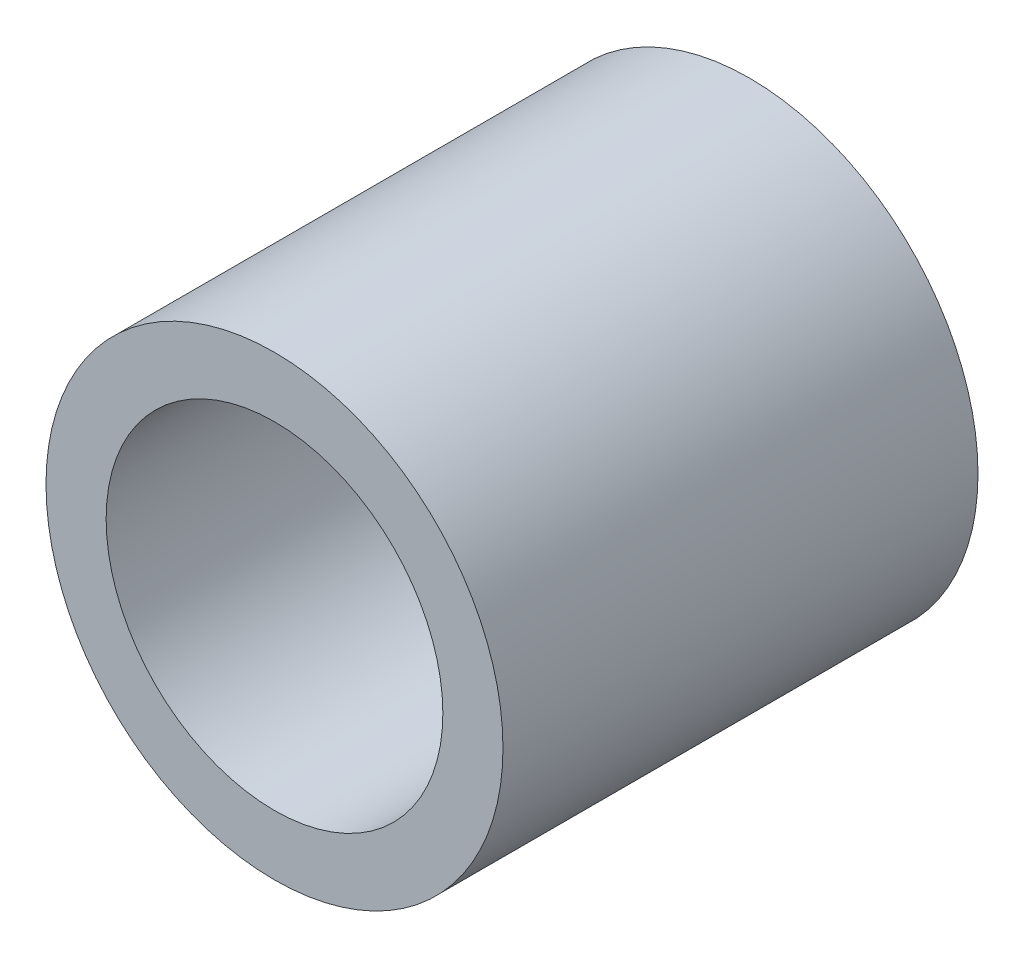
SolidWorks part; units mm, degrees
ref_plane "Front Plane" through (0, 0, 0) normal (0, 0, 1) x (1, 0, 0)
ref_plane "Top Plane" through (0, 0, 0) normal (0, 1, 0) x (1, 0, 0)
ref_plane "Right Plane" through (0, 0, 0) normal (1, 0, 0) x (0, 0, -1)
sketch "Sketch1" plane through (0, 0, 0) normal (0, 0, 1) x (1, 0, 0)
  circle A0 centre (0, 0) radius 4.826
  circle A1 centre (0, 0) radius 3.556
  dimension "D1" = 7.112
  dimension "D2" = 1.27
extrude "Boss-Extrude1" add sketch "Sketch1" along normal blind 10.033
